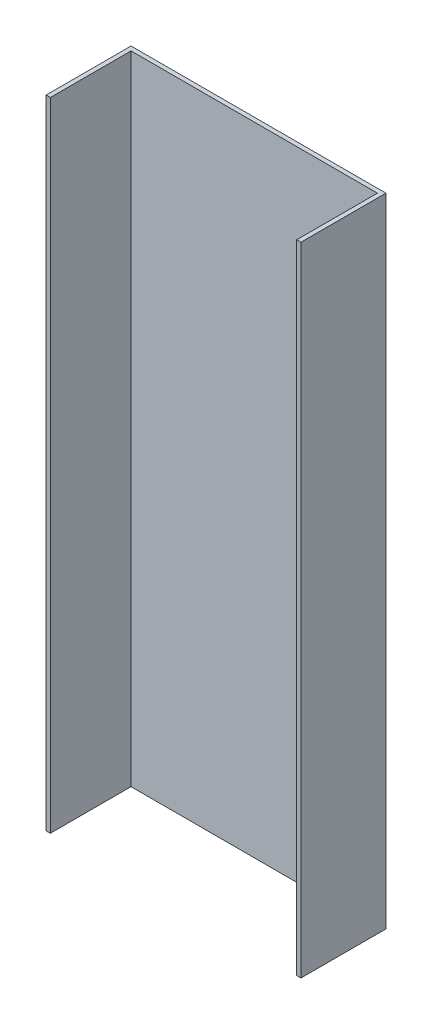
SolidWorks part; units mm, degrees
other "COLLMESH-Extrude-Thin2" parameters "Thickness"=3
ref_plane "Front Plane" through (0, 0, 0) normal (0, 0, 1) x (1, 0, 0)
ref_plane "Top Plane" through (0, 0, 0) normal (0, 1, 0) x (1, 0, 0)
ref_plane "Right Plane" through (0, 0, 0) normal (1, 0, 0) x (0, 0, -1)
sketch "Sketch2" plane through (0, 0, 0) normal (0, 0, 1) x (1, 0, 0)
  line L1 (-300, -750) -> (300, -750)
  line L2 (-300, -750) -> (-300, 750)
  line L3 (-300, 750) -> (300, 750)
  line L4 (300, -750) -> (300, 750)
  line L5 (-300, -750) -> (300, 750) construction
  line L6 (-300, 750) -> (300, -750) construction
  point P0 (0, 0)
  dimension "D1" = 1500
  dimension "D2" = 600
extrude "Boss-Extrude1" add sketch "Sketch2" along normal blind 10
sketch "Sketch5" plane through (0, 0, 0) normal (0, 0, -1) x (-1, 0, 0)
  line L0 (-300, -750) -> (-300, 750) construction
  line L1 (300, 750) -> (300, -750) construction
  line L2 (-300, -750) -> (-300, 750)
  line L3 (300, 750) -> (300, -750)
extrude "Extrude-Thin2" add sketch "Sketch5" against normal blind 200 thin
